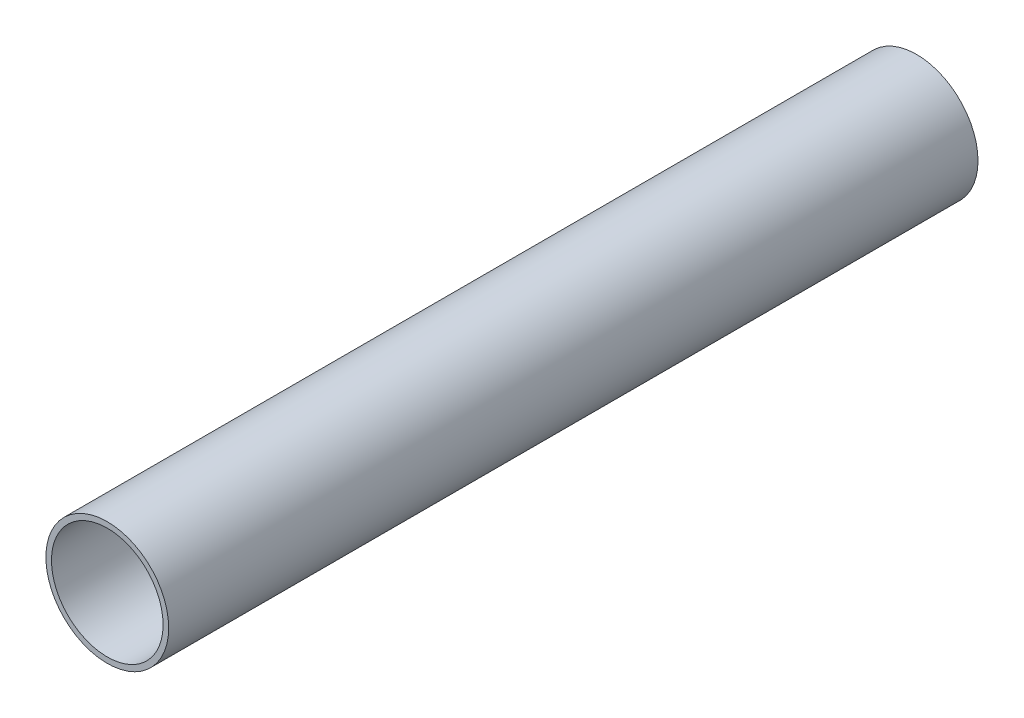
SolidWorks part; units mm, degrees
material "Сплав 2024"
ref_plane "Спереди" through (0, 0, 0) normal (0, 0, 1) x (1, 0, 0)
ref_plane "Сверху" through (0, 0, 0) normal (0, 1, 0) x (1, 0, 0)
ref_plane "Справа" through (0, 0, 0) normal (1, 0, 0) x (0, 0, -1)
sketch "Эскиз1" plane through (0, 0, 0) normal (0, 0, 1) x (1, 0, 0)
  circle A0 centre (0, 0) radius 11
  circle A1 centre (0, 0) radius 10
  dimension "D1" = 22
  dimension "D2" = 1
extrude "Бобышка-Вытянуть1" add sketch "Эскиз1" along normal blind 145
